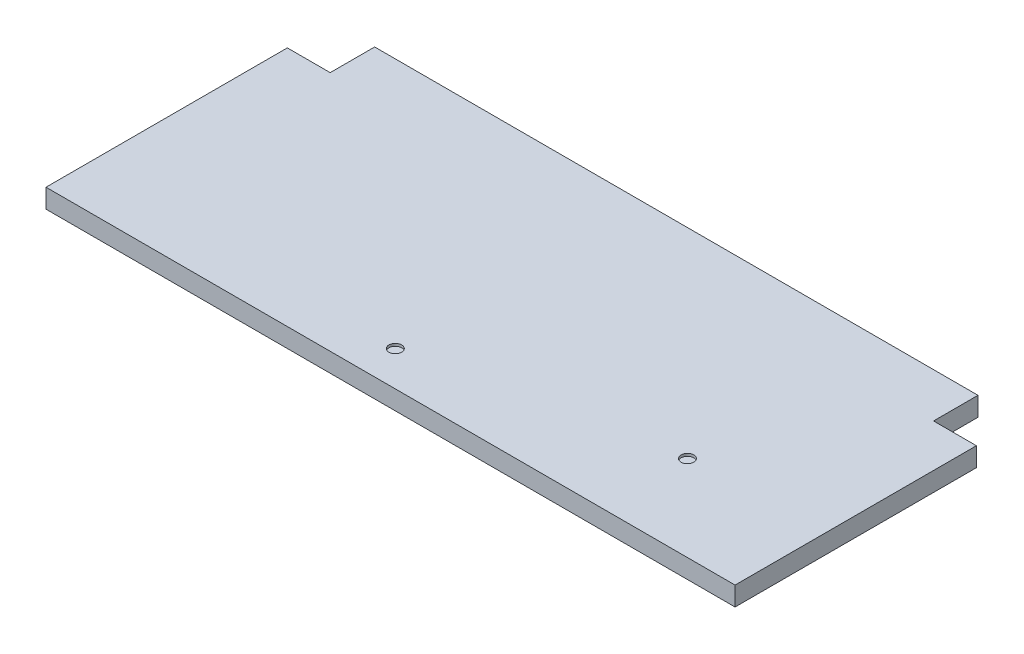
SolidWorks part; units mm, degrees
ref_plane "Front Plane" through (0, 0, 0) normal (0, 0, 1) x (1, 0, 0)
ref_plane "Top Plane" through (0, 0, 0) normal (0, 1, 0) x (1, 0, 0)
ref_plane "Right Plane" through (0, 0, 0) normal (1, 0, 0) x (0, 0, -1)
sketch "Sketch1" plane through (0, 0, 0) normal (0, 1, 0) x (1, 0, 0)
  line L0 (0, 0) -> (688.975, 0)
  line L1 (-55, 0) -> (55, 0) construction
  line L2 (688.975, 0) -> (688.975, 241.3)
  line L3 (688.975, 241.3) -> (646.1125, 241.3)
  line L4 (646.1125, 241.3) -> (646.1125, 285.75)
  line L5 (344.4875, 0) -> (344.4875, 169.0526) construction
  line L6 (42.8625, 241.3) -> (42.8625, 285.75)
  line L7 (0, 241.3) -> (42.8625, 241.3)
  line L8 (0, 0) -> (0, 241.3)
  line L9 (42.8625, 285.75) -> (646.1125, 285.75)
  dimension "D1" = 688.975
  dimension "D2" = 241.3
  dimension "D3" = 42.8625
  dimension "D4" = 44.45
extrude "Boss-Extrude1" add sketch "Sketch1" along normal blind 19.05
sketch "Sketch2" plane through (0, 19.05, 0) normal (0, 1, 0) x (1, 0, 0)
  line L0 (-10.4775, 0) -> (10.4775, 0) construction
  line L1 (688.975, 0) -> (688.975, 241.3) construction
  circle A0 centre (555.625, 85.725) radius 6.35
  dimension "D1" = 12.7
  dimension "D3" = 133.35
  dimension "D2" = 85.725
extrude "Cut-Extrude1" cut sketch "Sketch2" against normal blind 2.54
sketch "Sketch3" plane through (0, 19.05, 0) normal (0, 1, 0) x (1, 0, 0)
  line L1 (-10.4775, 0) -> (10.4775, 0) construction
  line L2 (688.975, 0) -> (688.975, 241.3) construction
  circle A0 centre (314.325, 34.925) radius 6.35
  dimension "D1" = 12.7
  dimension "D2" = 34.925
  dimension "D3" = 374.65
extrude "Cut-Extrude2" cut sketch "Sketch3" against normal blind 2.54
